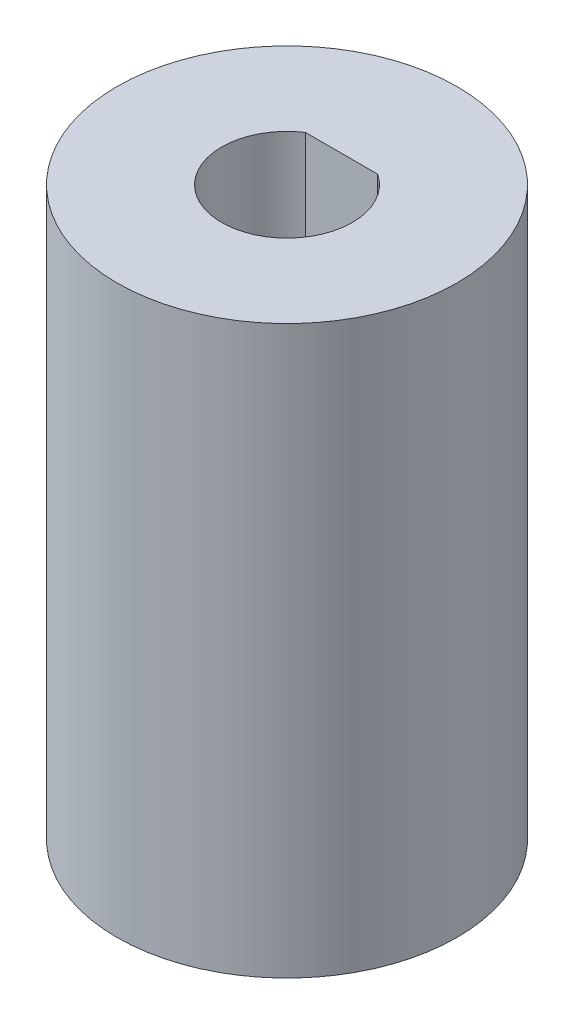
SolidWorks part; units mm, degrees
ref_plane "Front Plane" through (0, 0, 0) normal (0, 0, 1) x (1, 0, 0)
ref_plane "Top Plane" through (0, 0, 0) normal (0, 1, 0) x (1, 0, 0)
ref_plane "Right Plane" through (0, 0, 0) normal (1, 0, 0) x (0, 0, -1)
sketch "Sketch1" plane through (0, 0, 0) normal (0, 1, 0) x (1, 0, 0)
  circle A0 centre (0, 0) radius 7.8
  dimension "D1" = 15.6
extrude "Boss-Extrude1" add sketch "Sketch1" along normal blind 26
sketch "Sketch2" plane through (0, 0, 0) normal (0, 1, 0) x (1, 0, 0)
  line L0 (-1.6583, 2.5) -> (1.6583, 2.5)
  circle A1 centre (0, 0) radius 3
  point P6 (-1.6583, 2.5)
  point P7 (0, -3)
  dimension "D1" = 6
  dimension "D2" = 5.5
extrude "Cut-Extrude3" cut sketch "Sketch2" along normal through all contours L0 A1
